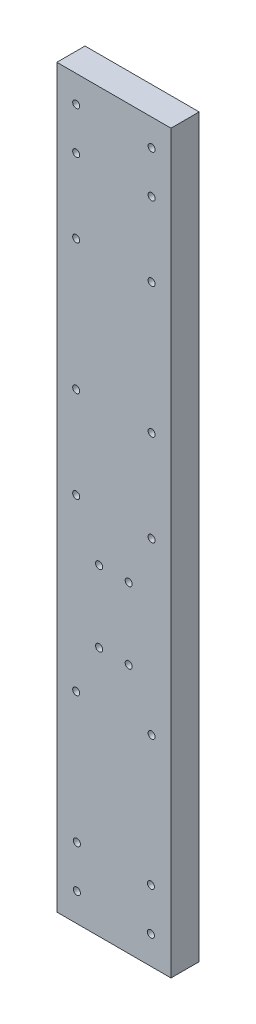
SolidWorks part; units mm, degrees
ref_plane "Front Plane" through (0, 0, 0) normal (0, 0, 1) x (1, 0, 0)
ref_plane "Top Plane" through (0, 0, 0) normal (0, 1, 0) x (1, 0, 0)
ref_plane "Right Plane" through (0, 0, 0) normal (1, 0, 0) x (0, 0, -1)
sketch "Sketch1" plane through (0, 0, 0) normal (0, 0, 1) x (1, 0, 0)
  line L0 (0, 104.46) -> (0, 0)
  line L1 (16.2, 104.46) -> (16.2, 0)
  line L2 (0, 104.46) -> (16.2, 104.46)
  line L3 (0, 0) -> (16.2, 0)
  line L4 (0, 55.14) -> (16.2, 55.14) construction
  line L5 (0, 14) -> (16.2, 14) construction
  line L6 (0, 26) -> (16.2, 26) construction
  line L7 (0, 86.665) -> (16.2, 86.665) construction
  line L8 (0, 63.14) -> (16.2, 63.14) construction
  line L10 (0, 92.665) -> (16.2, 92.665) construction
  circle A1 centre (13.45, 52.64) radius 0.5
  circle A2 centre (13.45, 94.665) radius 0.5
  circle A4 centre (2.75, 100.665) radius 0.5
  circle A6 centre (2.75, 52.64) radius 0.5
  circle A7 centre (6, 45.64) radius 0.5
  circle A8 centre (13.45, 28.5) radius 0.5
  circle A11 centre (6, 35.5) radius 0.5
  circle A13 centre (2.75, 28.5) radius 0.5
  circle A16 centre (2.75, 94.665) radius 0.5
  circle A17 centre (13.45, 84.165) radius 0.5
  circle A19 centre (13.45, 65.64) radius 0.5
  circle A20 centre (13.45, 100.665) radius 0.5
  circle A21 centre (10.2, 45.64) radius 0.5
  circle A22 centre (2.75, 84.165) radius 0.5
  circle A23 centre (2.85, 10) radius 0.5
  circle A24 centre (13.35, 10) radius 0.5
  circle A25 centre (13.35, 4) radius 0.5
  circle A26 centre (2.85, 4) radius 0.5
  circle A27 centre (2.75, 65.64) radius 0.5
  circle A30 centre (10.2, 35.5) radius 0.5
  dimension "D1" = 2.85
  dimension "D2" = 2.85
  dimension "D3" = 2.85
  dimension "D4" = 2.85
  dimension "D5" = 4
  dimension "D6" = 4
  dimension "D7" = 6
  dimension "D8" = 6
  dimension "D9" = 4
  dimension "D10" = 12
  dimension "D11" = 29.14
  dimension "D12" = 2.75
  dimension "D13" = 6
  dimension "D14" = 9.5
  dimension "D15" = 2.5
  dimension "D16" = 2.75
  dimension "D17" = 6
  dimension "D18" = 2.5
  dimension "D19" = 9.5
  dimension "D20" = 2.75
  dimension "D21" = 2.75
  dimension "D22" = 6
  dimension "D23" = 6
  dimension "D24" = 9.5
  dimension "D25" = 2.5
  dimension "D26" = 2.5
  dimension "D27" = 9.5
  dimension "D28" = 8
  dimension "D29" = 23.525
  dimension "D30" = 2.75
  dimension "D31" = 2.75
  dimension "D32" = 2.75
  dimension "D33" = 2.75
  dimension "D34" = 2.5
  dimension "D35" = 2.5
  dimension "D36" = 2.5
  dimension "D37" = 2.5
  dimension "D38" = 6
  dimension "D39" = 11.795
  dimension "D40" = 2.75
  dimension "D41" = 2.75
  dimension "D42" = 2.75
  dimension "D43" = 2.75
  dimension "D44" = 2
  dimension "D45" = 8
  dimension "D46" = 2
  dimension "D47" = 8
  dimension "D48" = 16.2
extrude "Boss-Extrude1" add sketch "Sketch1" along normal blind 4
equation "\"D11@Sketch1\"= \"HL@parametersSketch@prostheticParameters.SLDPRT\" * 0.244 - 4 - 12 'Ring PIP Length"
equation "\"D29@Sketch1\"= \"HL@parametersSketch@prostheticParameters.SLDPRT\" * 0.165 - 3 - 4 'Ring MIP Length"
equation "\"D39@Sketch1\"= \"HL@parametersSketch@prostheticParameters.SLDPRT\" * 0.107 - 3 - 5'Ring DIP Length - Fingertip"
equation "\"D48@Sketch1\"= \"fingerWidth@parametersSketch@prostheticParameters.SLDPRT\"'Ring Breadth"
